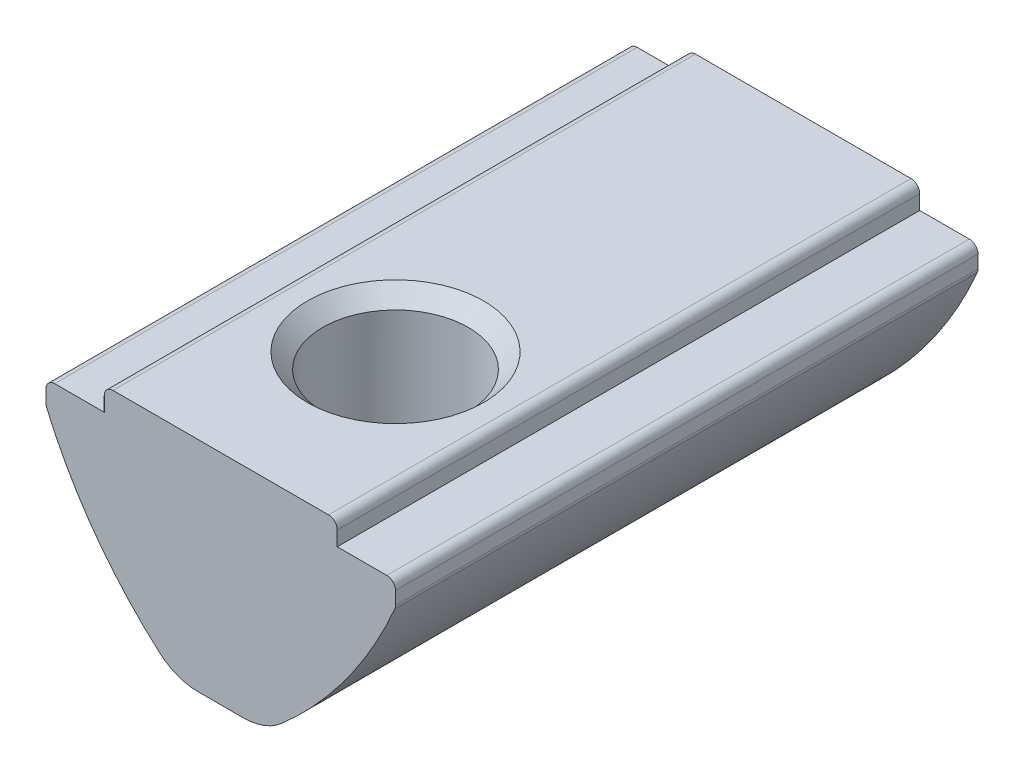
SolidWorks part; units mm, degrees
ref_plane "Спереди" through (0, 0, 0) normal (0, 0, 1) x (1, 0, 0)
ref_plane "Сверху" through (0, 0, 0) normal (0, 1, 0) x (1, 0, 0)
ref_plane "Справа" through (0, 0, 0) normal (1, 0, 0) x (0, 0, -1)
sketch "Эскиз1" plane through (0, 0, 0) normal (0, 0, 1) x (1, 0, 0)
  line L0 (-4, 0) -> (4, 0)
  line L5 (-4, 0) -> (-4, -0.8)
  line L6 (-4, -0.8) -> (-6, -0.8)
  line L7 (-6, -0.8) -> (-6, -1.6)
  line L8 (4, 0) -> (4, -0.8)
  line L9 (4, -0.8) -> (6, -0.8)
  line L10 (6, -0.8) -> (6, -1.6)
  line L11 (-1.5, -7.5) -> (1.5, -7.5)
  arc A0 (-6, -1.6) -> (-1.5, -7.5) centre (7.8062, 4.2641) ccw
  arc A1 (1.5, -7.5) -> (6, -1.6) centre (-7.8062, 4.2641) ccw
  point P0 (0, -7.5)
  point P4 (0, 0)
  dimension "D7" = 15
  dimension "D1" = 8
  dimension "D2" = 12
  dimension "D3" = 0.8
  dimension "D4" = 3
  dimension "D5" = 0.8
  dimension "D6" = 7.5
extrude "Бобышка-Вытянуть1" add sketch "Эскиз1" along normal mid plane 20
fillet "Скругление1" radius 0.3 6 edges at (6, -1.6, 0) (6, -0.8, 0) (-6, -0.8, 0) (-6, -1.6, 0) (4, 0, 0) (-4, 0, 0)
fillet "Скругление2" radius 2 2 edges at (1.5, -7.5, 0) (-1.5, -7.5, 0)
hole_wizard "Отверстие обработанное метчиком M61" positions "Эскиз2" profile "Эскиз4" tap size "M6" standard "ISO" end condition through all
sketch "Эскиз2" plane through (0, 0, 0) normal (0, 1, 0) x (1, 0, 0)
  line L0 (3.7, -10) -> (-3.7, -10) construction
  point P0 (0, -4)
  dimension "D1" = 6
sketch "Эскиз4" plane through (0, 0, 4) normal (1, 0, 0) x (0, 0, 1)
  line L0 (0, 0) -> (0, 7.5)
  line L1 (0, 7.5) -> (2.5, 7.5)
  line L2 (2.5, 7.5) -> (2.5, 0.525)
  line L3 (2.5, 0.525) -> (3.025, 0)
  line L5 (3.025, 0) -> (0, 0)
  line L6 (-2.5, 0.525) -> (-3.025, 0) construction
  line L11 (0, -6.35) -> (0, 107.95) construction
  dimension "Диаметр проходного сверла" = 5
  dimension "Глубина проходного сверла" = 7.5
  dimension "Диаметр передней зенковки" = 6.05
  dimension "Угол передней зенковки" = 90
cosmetic thread "Отверстие резьбы1" parameters "D2"=6
sketch "Эскиз5" plane through (0, 0, 0) normal (1, 0, 0) x (0, 0, -1)
  line L1 (6, -4.3) -> (6, -8.3) construction
  line L2 (10, -7.0022) -> (10, -1.657) construction
  line L3 (6, -4.3) -> (6, -8.3)
  line L5 (10, -7.5) -> (-1.6236, -7.5) construction
  arc A0 (6, -4.3) -> (6, -8.3) centre (6, -6.3) ccw
  point P3 (4, -7.4722)
  dimension "D3" = 2
  dimension "D1" = 0.8
  dimension "D2" = 4
revolve "Повернуть1" add sketch "Эскиз5" angle 360 about L1
